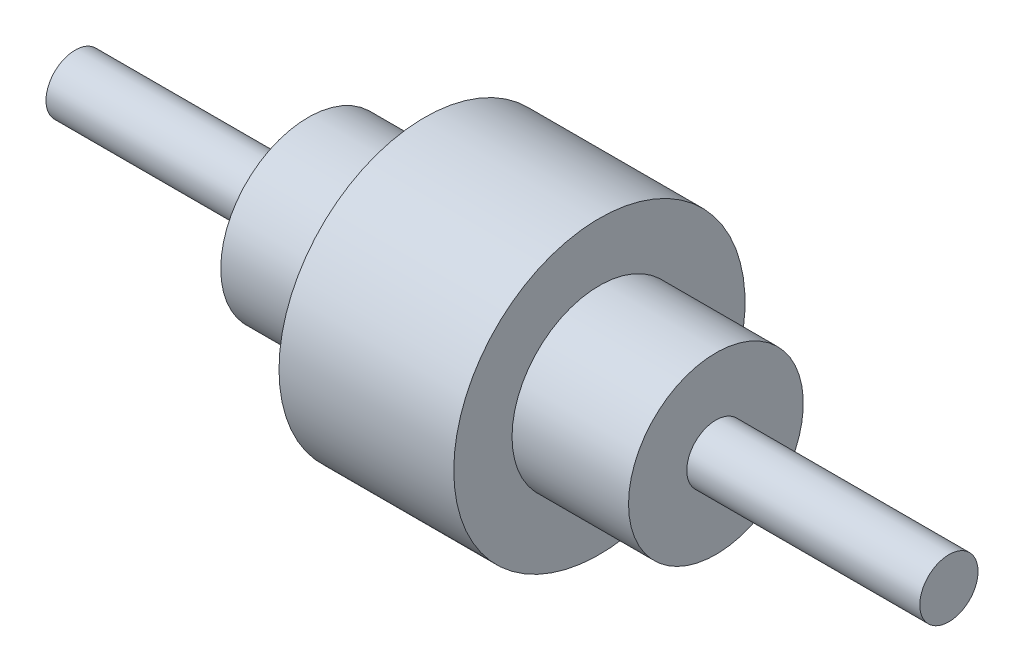
SolidWorks part; units mm, degrees
ref_plane "Front Plane" through (0, 0, 0) normal (0, 0, 1) x (1, 0, 0)
ref_plane "Top Plane" through (0, 0, 0) normal (0, 1, 0) x (1, 0, 0)
ref_plane "Right Plane" through (0, 0, 0) normal (1, 0, 0) x (0, 0, -1)
sketch "Sketch1" plane through (0, 0, 0) normal (0, 0, 1) x (1, 0, 0)
  line L0 (0, 0) -> (10198.2546, 0) construction
  line L1 (0, 0) -> (0, 5454.7402) construction
  line L2 (0, 0) -> (0.0001, 0)
  line L3 (0, 0) -> (0, 254)
  line L4 (0, 254) -> (2032, 254)
  line L5 (2032, 254) -> (2032, 762)
  line L6 (2032, 762) -> (3048, 762)
  line L7 (3048, 762) -> (3048, 1270)
  line L8 (3048, 1270) -> (4572, 1270)
  line L9 (3810, 1270) -> (3810, 5313.4915) construction
  line L10 (3810, 1270) -> (3810, -2895.7419) construction
  line L11 (4572, 762) -> (4572, 1270)
  line L12 (5588, 762) -> (4572, 762)
  line L13 (5588, 254) -> (5588, 762)
  line L14 (7620, 254) -> (5588, 254)
  line L15 (7620, 0) -> (7620, 254)
  line L16 (0.0001, 0) -> (7620, 0)
  dimension "D1" = 508
  dimension "D2" = 2032
  dimension "D3" = 1016
  dimension "D4" = 762
  dimension "D5" = 1524
  dimension "D6" = 2540
  dimension "D7" = 7619.9999
revolve "Revolve4" add sketch "Sketch1" angle 360 about L0
